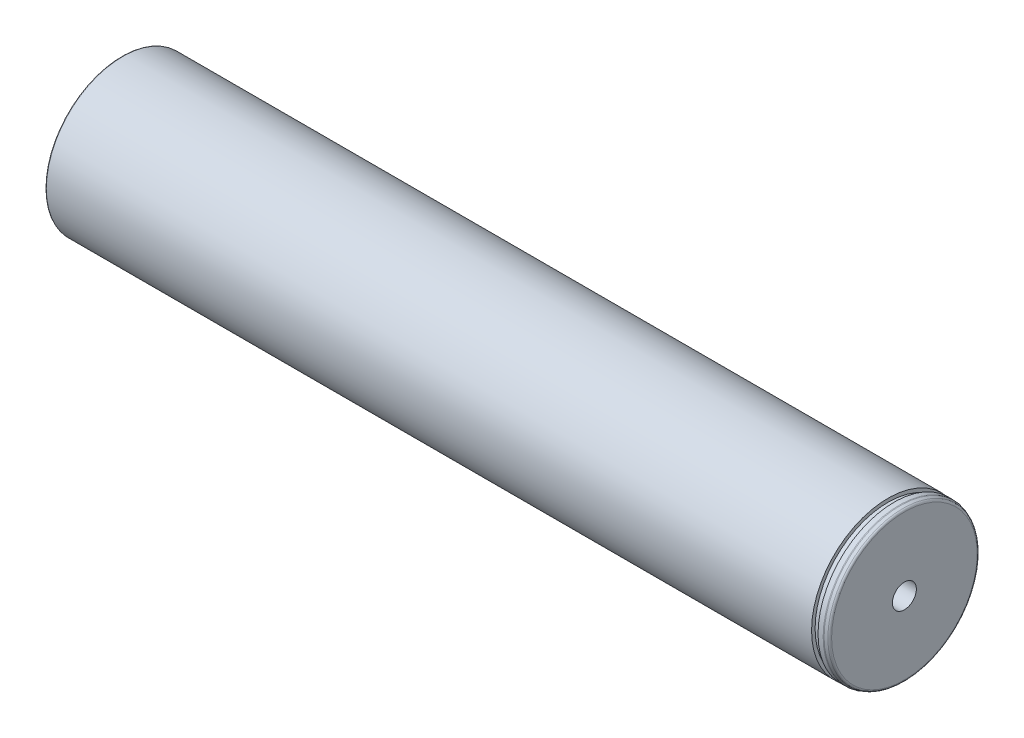
SolidWorks part; units mm, degrees
revolve "Base-Revolve" add sketch "Sketch1" angle 360 about L0
sketch "Sketch1" plane through (0, 0, 0) normal (0, 0, 1) x (1, 0, 0)
  line L0 (-168, 0) -> (170, 0) construction
  line L1 (163, 32.5) -> (0, 32.5)
  line L2 (163, 32.5) -> (163, 31)
  line L4 (-145.0555, 0) -> (147.0555, 0)
  line L5 (169.342, 31.9115) -> (168.1657, 32.3397)
  line L6 (-163, 32.1) -> (-163, 28.4)
  line L7 (-168, 5.1) -> (-148, 5.1)
  line L8 (-148, 5.1) -> (-145.0555, 0)
  line L9 (170, 5.1) -> (150, 5.1)
  line L10 (150, 5.1) -> (147.0555, 0)
  line L13 (0, 32.5) -> (-162.6, 32.5)
  line L17 (-164.2, 24.8845) -> (-167.8, 22.8061)
  line L19 (-164, 28) -> (-164, 25.2309)
  line L20 (-168, 22.4597) -> (-168, 5.1)
  line L21 (-163.4, 28) -> (-164, 28)
  line L22 (170, 30.9719) -> (170, 5.1)
  line L23 (165.65, 32.4) -> (167.8237, 32.4)
  line L24 (165.65, 31) -> (165.65, 32.4)
  line L25 (163, 31) -> (165.65, 31)
  arc A0 (170, 30.9719) -> (169.342, 31.9115) centre (169, 30.9719) ccw
  arc A1 (-163.4, 28) -> (-163, 28.4) centre (-163.4, 28.4) ccw
  arc A2 (167.8237, 32.4) -> (168.1657, 32.3397) centre (167.8237, 31.4) cw
  arc A3 (-167.8, 22.8061) -> (-168, 22.4597) centre (-167.6, 22.4597) ccw
  arc A4 (-164.2, 24.8845) -> (-164, 25.2309) centre (-164.4, 25.2309) ccw
  arc A5 (-163, 32.1) -> (-162.6, 32.5) centre (-162.6, 32.1) cw
  point P15 (168, 32.4)
  point P28 (-164, 25)
  point P31 (-163, 32.5)
  dimension "D11" = 50
  dimension "D6" = 2
  dimension "D16" = 20
  dimension "D17" = 1
  dimension "D19" = 0.4
  dimension "D2" = 64.8
  dimension "D3" = 62
  dimension "D4" = 2.65
  dimension "D5" = 7
  dimension "D7" = 5
  dimension "D8" = 1
  dimension "D9" = 56
  dimension "D10" = 30
  dimension "D12" = 65
  dimension "D13" = 163
  dimension "D14" = 326
  dimension "D20" = 10.2
  dimension "D21" = 20
  dimension "D22" = 60
  dimension "D23" = 10.2
  dimension "D24" = 20
  dimension "D25" = 60
cosmetic thread "Cosmetic Thread1"
cosmetic thread "Cosmetic Thread2"
ref_plane "Front" through (0, 0, 0) normal (0, 0, 1) x (1, 0, 0)
ref_plane "Top" through (0, 0, 0) normal (0, 1, 0) x (1, 0, 0)
ref_plane "Right" through (0, 0, 0) normal (1, 0, 0) x (0, 0, -1)
